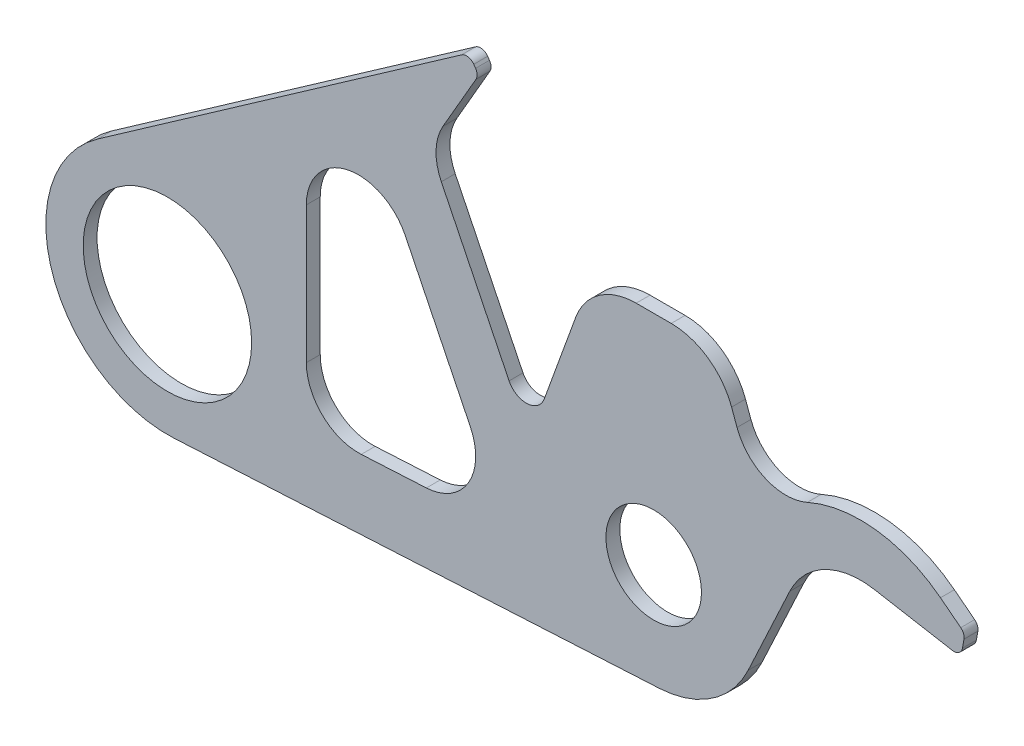
SolidWorks part; units mm, degrees
ref_plane "Plane1" through (0, 0, 0) normal (0, 0, 1) x (1, 0, 0)
ref_plane "Plane2" through (0, 0, 0) normal (0, 1, 0) x (1, 0, 0)
ref_plane "Plane3" through (0, 0, 0) normal (1, 0, 0) x (0, 0, -1)
sketch "Sketch1" plane through (0, 0, 0) normal (0, 0, 1) x (1, 0, 0)
  line L0 (0, 0) -> (210, 0) construction
  line L1 (456.811, 62.1514) -> (445.1375, 71.2223)
  line L5 (111.6064, -24.0585) -> (149.1064, -22.0476)
  line L6 (174.4479, 21.0931) -> (136.9479, 97.7437)
  line L7 (80, 84.5599) -> (80, 5.8985)
  line L13 (-40.1504, 57.3406) -> (169.4377, 204.0958)
  line L14 (283.2127, -54.9139) -> (3.7482, -69.8996)
  line L15 (358.335, 31.0178) -> (334.3785, -20.3571)
  line L16 (452.009, 48.3682) -> (406.933, 56.3163)
  line L20 (176.4013, 202.8679) -> (177.4422, 201.3814)
  line L21 (177.6765, 196.0135) -> (158.6843, 163.118)
  line L22 (157.7172, 134.9342) -> (196.7435, 55.1638)
  line L23 (216.9701, 56.2361) -> (235.1391, 106.1547)
  line L24 (280, 5) -> (280, 130.5) construction
  line L25 (269.9077, 130.5) -> (290.0923, 130.5)
  line L26 (324.8609, 106.1547) -> (327.9897, 97.5585)
  line L27 (457.8012, 52.424) -> (458.6672, 57.335)
  circle A0 centre (0, 0) radius 48.5
  circle A1 centre (280, 5) radius 27.5
  arc A2 (445.1375, 71.2223) -> (368.4486, 80.4422) centre (399.1188, 12) ccw
  arc A3 (327.9897, 97.5585) -> (368.4486, 80.4422) centre (356.1805, 107.8191) ccw
  arc A4 (458.6672, 57.335) -> (456.811, 62.1514) centre (453.7431, 58.2032) ccw
  arc A6 (149.1064, -22.0476) -> (174.4479, 21.0931) centre (147.5, 7.9094) ccw
  arc A7 (136.9479, 97.7437) -> (80, 84.5599) centre (110, 84.5599) ccw
  arc A8 (80, 5.8985) -> (111.6064, -24.0585) centre (110, 5.8985) ccw
  arc A14 (-40.1504, 57.3406) -> (3.7482, -69.8996) centre (0, 0) ccw
  arc A16 (283.2127, -54.9139) -> (334.3785, -20.3571) centre (280, 5) ccw
  arc A17 (406.933, 56.3163) -> (358.335, 31.0178) centre (399.1188, 12) ccw
  arc A18 (176.4013, 202.8679) -> (169.4377, 204.0958) centre (172.3056, 200) ccw
  arc A19 (452.009, 48.3682) -> (457.8012, 52.424) centre (452.8772, 53.2923) ccw
  arc A20 (158.6843, 163.118) -> (157.7172, 134.9342) centre (184.665, 148.118) ccw
  arc A21 (196.7435, 55.1638) -> (216.9701, 56.2361) centre (206.6289, 60) ccw
  arc A25 (324.8609, 106.1547) -> (290.0923, 130.5) centre (290.0923, 93.5) ccw
  arc A26 (269.9077, 130.5) -> (235.1391, 106.1547) centre (269.9077, 93.5) ccw
  arc A27 (177.6765, 196.0135) -> (177.4422, 201.3814) centre (173.3464, 198.5135) ccw
  point P0 (456.933, 47.5)
  point P23 (459.1904, 60.3025)
  point P47 (316, 130.5)
  point P51 (244, 130.5)
  point P54 (179.2692, 198.7721)
  dimension "D3" = 97
  dimension "D4" = 55
  dimension "D6" = 5
  dimension "D7" = 10
  dimension "D9" = 205
  dimension "D11" = 30
  dimension "D17" = 30
  dimension "D18" = 52
  dimension "D19" = 5
  dimension "D20" = 13
  dimension "D22" = 37
  dimension "D23" = 40
  dimension "D24" = 5
  dimension "D25" = 275
  dimension "D27" = 30
  dimension "D30" = 70
  dimension "D31" = 60
  dimension "D33" = 45
  dimension "D35" = 42.5
  dimension "D16" = 75
  dimension "D1" = 280
  dimension "D5" = 35
  dimension "D8" = 25
  dimension "D10" = 35
  dimension "D12" = 125.5
  dimension "D13" = 72
  dimension "D14" = 20
  dimension "D15" = 20
  dimension "D21" = 60
  dimension "D26" = 67
  dimension "D28" = 80
  dimension "D29" = 97.5
  dimension "D32" = 65
  dimension "D34" = 10
  dimension "D36" = 5
extrude "Base-Extrude" add sketch "Sketch1" along normal blind 8
